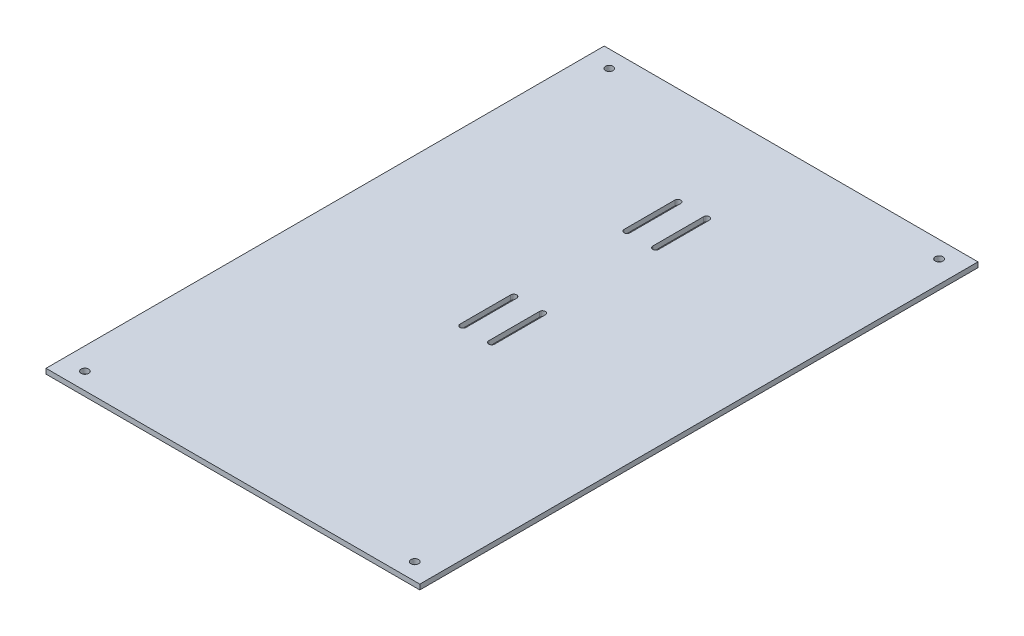
SolidWorks part; units mm, degrees
ref_plane "Front Plane" through (0, 0, 0) normal (0, 0, 1) x (1, 0, 0)
ref_plane "Top Plane" through (0, 0, 0) normal (0, 1, 0) x (1, 0, 0)
ref_plane "Right Plane" through (0, 0, 0) normal (1, 0, 0) x (0, 0, -1)
sketch "Sketch1" plane through (0, 0, 0) normal (1, 0, 0) x (0, 0, -1)
  line L0 (-207.5, -13) -> (122.5, -13)
extrude "Extrude-Thin1" add sketch "Sketch1" along normal up to vertex (110.5 mm away) and the other way up to vertex (110.5 mm away) thin thin type one direction reverse wall 3
sketch "Sketch2" plane through (0, -13, 0) normal (0, -1, 0) x (1, 0, 0)
  line L0 (-8.9932, -34.5) -> (-8.9932, -64.5) construction
  line L1 (-7.2432, -34.5) -> (-7.2432, -64.5)
  line L2 (-10.7432, -34.5) -> (-10.7432, -64.5)
  line L3 (8.0068, -34.5) -> (8.0068, -64.5) construction
  line L4 (9.7568, -34.5) -> (9.7568, -64.5)
  line L5 (6.2568, -34.5) -> (6.2568, -64.5)
  line L6 (8.0068, 62.5) -> (8.0068, 32.5) construction
  line L7 (9.7568, 62.5) -> (9.7568, 32.5)
  line L8 (6.2568, 62.5) -> (6.2568, 32.5)
  line L9 (-8.9932, 62.5) -> (-8.9932, 32.5) construction
  line L10 (-7.2432, 62.5) -> (-7.2432, 32.5)
  line L11 (-10.7432, 62.5) -> (-10.7432, 32.5)
  line L12 (-110.5, 207.5) -> (-110.5, -122.5) construction
  arc A0 (-7.2432, -34.5) -> (-10.7432, -34.5) centre (-8.9932, -34.5) ccw
  arc A1 (-10.7432, -64.5) -> (-7.2432, -64.5) centre (-8.9932, -64.5) ccw
  arc A2 (9.7568, -34.5) -> (6.2568, -34.5) centre (8.0068, -34.5) ccw
  arc A3 (6.2568, -64.5) -> (9.7568, -64.5) centre (8.0068, -64.5) ccw
  arc A4 (9.7568, 62.5) -> (6.2568, 62.5) centre (8.0068, 62.5) ccw
  arc A5 (6.2568, 32.5) -> (9.7568, 32.5) centre (8.0068, 32.5) ccw
  arc A6 (-7.2432, 62.5) -> (-10.7432, 62.5) centre (-8.9932, 62.5) ccw
  arc A7 (-10.7432, 32.5) -> (-7.2432, 32.5) centre (-8.9932, 32.5) ccw
  circle A8 centre (97.5, -112.5) radius 2.1
  circle A9 centre (-97.5, -112.5) radius 2.1
  circle A10 centre (97.5, 197.5) radius 2.1
  circle A11 centre (-97.5, 197.5) radius 2.1
  point P2 (-8.9932, -49.5)
  point P9 (8.0068, -49.5)
  point P17 (8.0068, 47.5)
  point P25 (-8.9932, 47.5)
  dimension "D2" = 1.75
  dimension "D3" = 4.2
  dimension "D1" = 30
  dimension "D4" = 310
  dimension "D5" = 13
extrude "Cut-Extrude1" cut sketch "Sketch2" against normal up to next
hole_wizard "M4 Clearance Hole1" positions "Sketch3" profile "Sketch4" hole size "M4" standard "ISO" end condition through all
sketch "Sketch3" plane through (0, -13, 0) normal (0, 1, 0) x (1, 0, 0)
  point P0 (-97.5, -197.5)
  point P3 (97.5, -197.5)
  point P6 (97.5, 112.5)
  point P9 (-97.5, 112.5)
sketch "Sketch4" plane through (-97.5, -13, 197.5) normal (1, 0, 0) x (0, 0, -1)
  line L0 (0, 0) -> (0, 3)
  line L1 (0, 3) -> (2.25, 3)
  line L2 (2.25, 3) -> (2.25, 0)
  line L5 (2.25, 0) -> (0, 0)
  line L11 (0, -6.35) -> (0, 107.95) construction
  dimension "Thru Hole Dia." = 4.5
  dimension "Thru Hole Depth" = 3
